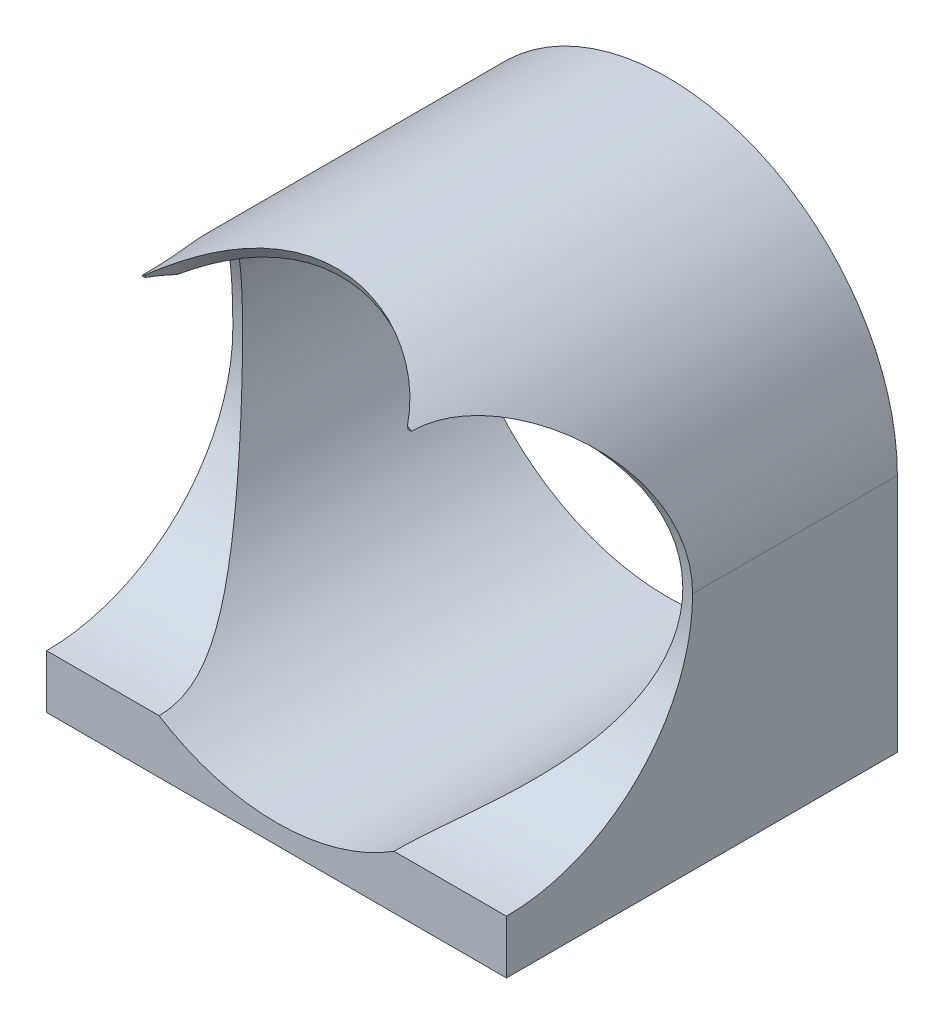
SolidWorks part; units mm, degrees
ref_plane "Front Plane" through (0, 0, 0) normal (0, 0, 1) x (1, 0, 0)
ref_plane "Top Plane" through (0, 0, 0) normal (0, 1, 0) x (1, 0, 0)
ref_plane "Right Plane" through (0, 0, 0) normal (1, 0, 0) x (0, 0, -1)
sketch "Sketch1" plane through (0, 0, 0) normal (0, 0, 1) x (1, 0, 0)
  circle A0 centre (0, 0) radius 22.225 construction
  circle A1 centre (0, 0) radius 22.225 construction
  circle A2 centre (0, 0) radius 23.525
  circle A3 centre (0, 0) radius 22.525
  dimension "D1" = 1.3
  dimension "D2" = 0.3
extrude "Boss-Extrude1" add sketch "Sketch1" against normal blind 40
sketch "Sketch5" plane through (0, 0, -40) normal (0, 0, -1) x (-1, 0, 0)
  line L0 (23.525, 0) -> (23.525, -23.525)
  line L1 (23.525, -23.525) -> (0, -23.525)
  line L2 (0, -23.525) -> (-23.525, -23.525)
  line L3 (-23.525, -23.525) -> (-23.525, 0)
  line L5 (-23.525, -23.525) -> (23.525, -23.525)
  line L6 (-23.525, -23.525) -> (-23.525, -24.525)
  line L7 (-23.525, -24.525) -> (23.525, -24.525)
  line L8 (23.525, -23.525) -> (23.525, -24.525)
  circle A0 centre (0, 0) radius 23.525 construction
  circle M4 centre (0, 0) radius 23.525
  dimension "D1" = 1
extrude "Boss-Extrude2" add sketch "Sketch5" against normal blind 40 contours L3 L2 M4 | L1 L0 M4 | L8 L1 L2 L6 L7
sketch "Sketch2" plane through (34.5, 0, 0) normal (1, 0, 0) x (0, 0, -1)
  circle A0 centre (0, 0) radius 19.05 construction
  circle A1 centre (0, 0) radius 19.05
extrude "Cut-Extrude1" cut sketch "Sketch2" against normal through all
sketch "Sketch4" plane through (0, 0, 0) normal (0, -0.8988, -0.4384) x (1, 0, 0)
  circle A0 centre (0, 0) radius 15.85 construction
  circle A1 centre (0, 0) radius 15.85
extrude "Cut-Extrude2" cut sketch "Sketch4" against normal through all
